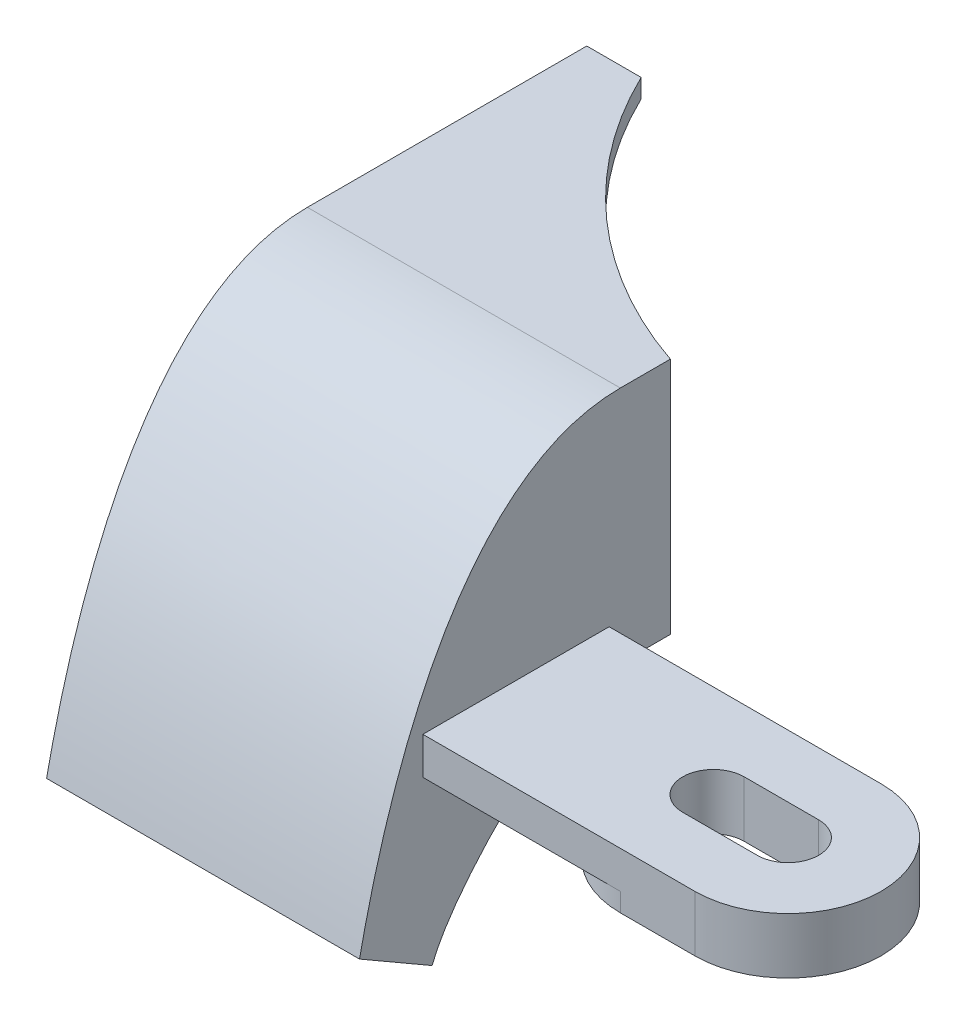
SolidWorks part; units mm, degrees
ref_plane "Plano frontal" through (0, 0, 0) normal (0, 0, 1) x (1, 0, 0)
ref_plane "Plano superior" through (0, 0, 0) normal (0, 1, 0) x (1, 0, 0)
ref_plane "Plano direito" through (0, 0, 0) normal (1, 0, 0) x (0, 0, -1)
sketch "Esboço1" plane through (0, 0, 0) normal (0, 0, 1) x (1, 0, 0)
  line L1 (-8.4, 6.4) -> (8.4, 6.4)
  line L2 (-8.4, 6.4) -> (-8.4, -6.4)
  line L3 (-8.4, -6.4) -> (8.4, -6.4)
  line L4 (8.4, 6.4) -> (8.4, -6.4)
  line L5 (-8.4, 6.4) -> (8.4, -6.4) construction
  line L6 (-8.4, -6.4) -> (8.4, 6.4) construction
  point P0 (0, 0)
  dimension "D1" = 12.8
  dimension "D2" = 16.8
extrude "Ressalto-extrusão1" add sketch "Esboço1" along normal blind 15
sketch "Esboço2" plane through (8.4, 0, 0) normal (1, 0, 0) x (0, 0, -1)
  line L0 (-15, -6.4) -> (0, -6.4) construction
  line L1 (-18.6376, -6.4) -> (-11.3604, -6.4) construction
  line L2 (-25.1029, -15.4) -> (-29, -13.15)
  line L3 (-15, 6.4) -> (-15, -6.4)
  line L6 (-15, 6.4) -> (0, 6.4) construction
  line L7 (-21.1788, 6.4) -> (-8.8176, 6.4) construction
  spline S0 degree 3 poles (-15, 6.4) (-24.57, 6.4) (-28.0693, -8.7492) (-29, -13.15) knots 0 0 0 0 1 1 1 1
  spline S1 degree 3 poles (-15, -6.4) (-18.0322, -6.4) (-23.9448, -12.2979) (-25.1029, -15.4) knots 0 0 0 0 1 1 1 1
  dimension "D1" = 14
  dimension "D2" = 9
  dimension "D3" = 4.5
  dimension "D4" = 30
extrude "Ressalto-extrusão2" add sketch "Esboço2" against normal through all
shell "Casca1" thickness 1
sketch "Esboço5" plane through (0, 6.4, 0) normal (0, 1, 0) x (1, 0, 0)
  circle A0 centre (16.15, 10.4) radius 24
  dimension "D1" = 48
  dimension "D2" = 7.75
  dimension "D3" = 10.4
extrude "Corte-extrusão1" cut sketch "Esboço5" against normal through all
sketch "Esboço6" plane through (0, -6.4, 0) normal (0, -1, 0) x (1, 0, 0)
  line L0 (23, 25.6) -> (8.4, 25.6)
  line L1 (8.4, 15) -> (8.4, 29) construction
  line L2 (8.4, 25.6) -> (8.4, 15.6)
  line L3 (8.4, 15.6) -> (23, 15.6)
  line L4 (19, 22.25) -> (23, 22.25)
  line L6 (19, 18.95) -> (23, 18.95)
  arc A0 (23, 18.95) -> (23, 22.25) centre (23, 20.6) ccw
  arc A1 (23, 15.6) -> (23, 25.6) centre (23, 20.6) ccw
  arc A2 (19, 22.25) -> (19, 18.95) centre (19, 20.6) ccw
  dimension "D1" = 3.3
  dimension "D4" = 5
  dimension "D2" = 20.6
  dimension "D3" = 23
  dimension "D5" = 4
extrude "Ressalto-extrusão3" add sketch "Esboço6" against normal blind 2
sketch "Esboço7" plane through (0, -6.4, 0) normal (0, -1, 0) x (1, 0, 0)
  line L0 (19, 18.95) -> (23, 18.95) construction
  line L1 (23, 22.25) -> (19, 22.25) construction
  line L2 (19, 18.95) -> (23, 18.95)
  line L3 (23, 22.25) -> (19, 22.25)
  line L4 (19, 20.6) -> (23, 20.6) construction
  line L5 (19, 25.6) -> (23, 25.6)
  line L6 (19, 15.6) -> (23, 15.6)
  arc A0 (19, 22.25) -> (19, 18.95) centre (19, 20.6) ccw construction
  arc A1 (23, 18.95) -> (23, 22.25) centre (23, 20.6) ccw construction
  arc A5 (19, 22.25) -> (19, 18.95) centre (19, 20.6) ccw
  arc A6 (23, 18.95) -> (23, 22.25) centre (23, 20.6) ccw
  arc A7 (19, 25.6) -> (19, 15.6) centre (19, 20.6) ccw
  arc A8 (23, 15.6) -> (23, 25.6) centre (23, 20.6) ccw
  arc A9 (23, 15.6) -> (23, 25.6) centre (23, 20.6) ccw construction
  point P6 (21, 20.6)
extrude "Ressalto-extrusão4" add sketch "Esboço7" along normal blind 1
